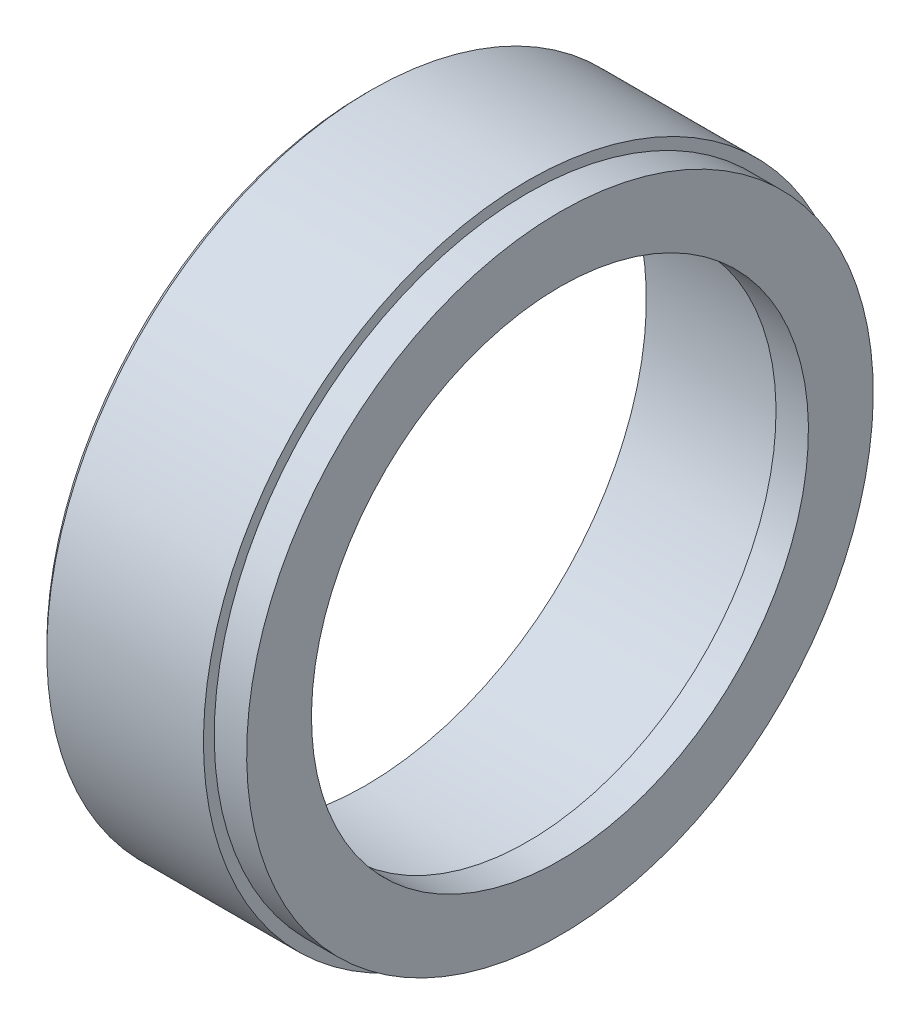
SolidWorks part; units mm, degrees
material "AISI 1020 Сталь, холоднокатаная"
ref_plane "Спереди" through (0, 0, 0) normal (0, 0, 1) x (1, 0, 0)
ref_plane "Сверху" through (0, 0, 0) normal (0, 1, 0) x (1, 0, 0)
ref_plane "Справа" through (0, 0, 0) normal (1, 0, 0) x (0, 0, -1)
sketch "Эскиз1" plane through (0, 0, 0) normal (0, 0, 1) x (1, 0, 0)
  line L0 (-108.55, 0) -> (-136.2738, 0) construction
  line L1 (-98.05, 23) -> (-101.05, 23)
  line L2 (-101.05, 23) -> (-101.05, 26)
  line L3 (-101.05, 26) -> (-116.05, 26)
  line L4 (-116.05, 26) -> (-116.05, 30)
  line L5 (-116.05, 30) -> (-101.05, 30)
  line L6 (-101.05, 30) -> (-101.05, 29)
  line L7 (-101.05, 29) -> (-98.05, 29)
  line L8 (-98.05, 29) -> (-98.05, 23)
  line L9 (-101.05, 55) -> (-101.05, 7.283) construction
  line L10 (-98.05, 55) -> (-98.05, 7.283) construction
  line L11 (-98.05, 29) -> (-101.05, 29) construction
  line L12 (-116.05, 24.5) -> (-116.05, -24.5) construction
  point P15 (-99.55, 23)
  dimension "D1" = 3
  dimension "D2" = 1
revolve "Повернуть1" add sketch "Эскиз1" angle 360 about L0
chamfer "Фаска1" distance 0.5 angle 45 1 edges at (-116.05, 30, 0)
